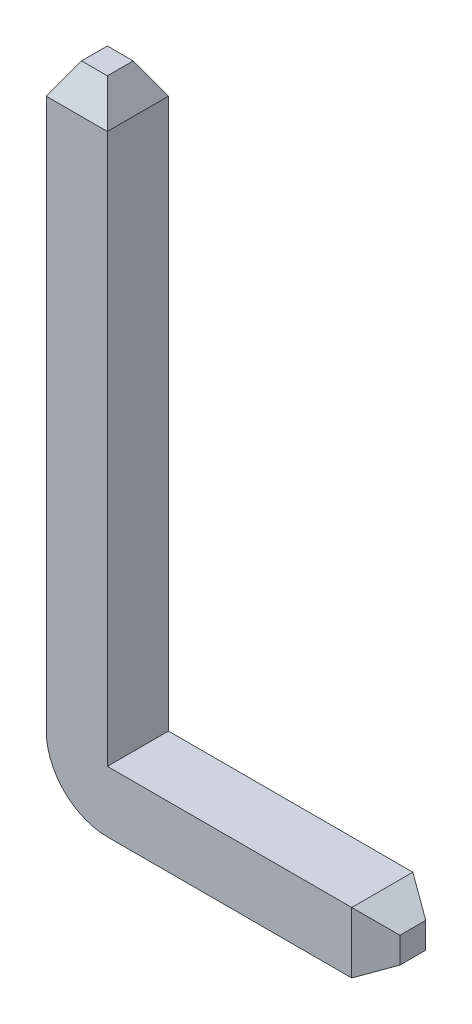
SolidWorks part; units mm, degrees
ref_plane "Front Plane" through (0, 0, 0) normal (0, 0, 1) x (1, 0, 0)
ref_plane "Top Plane" through (0, 0, 0) normal (0, 1, 0) x (1, 0, 0)
ref_plane "Right Plane" through (0, 0, 0) normal (1, 0, 0) x (0, 0, -1)
sketch "Sketch1" plane through (0, 0, 0) normal (0, 0, 1) x (1, 0, 0)
  line L0 (0, 0.2) -> (0, 4)
  line L1 (0.2, 0) -> (2, 0)
  line L2 (0, 0) -> (3.9001, 0) construction
  line L3 (0, 0) -> (0, 5.0149) construction
  arc A0 (0, 0.2) -> (0.2, 0) centre (0.2, 0.2) ccw
  dimension "D1" = 2
  dimension "D2" = 4
  dimension "D3" = 0.2
ref_plane "Plane1" through (0, 4, 0) normal (0, 1, 0) x (1, 0, 0)
sketch "Sketch2" plane through (0, 4, 0) normal (0, 1, 0) x (1, 0, 0)
  line L1 (-0.2, -0.2) -> (0.2, -0.2)
  line L2 (-0.2, -0.2) -> (-0.2, 0.2)
  line L3 (-0.2, 0.2) -> (0.2, 0.2)
  line L4 (0.2, -0.2) -> (0.2, 0.2)
  line L5 (-0.2, -0.2) -> (0.2, 0.2) construction
  line L6 (-0.2, 0.2) -> (0.2, -0.2) construction
  point P0 (0, 0)
  dimension "D1" = 0.4
  dimension "D2" = 0.4
sweep "Sweep1" add profiles "Sketch2" path "Sketch1"
chamfer "Chamfer1" distance 0.2 angle 30 4 edges at (0, 4, -0.2) (0, 4, 0.2) (-0.2, 4, 0) (0.2, 4, 0)
chamfer "Chamfer2" distance 0.2 angle 30 4 edges at (2, 0, -0.2) (2, -0.2, 0) (2, 0, 0.2) (2, 0.2, 0)
